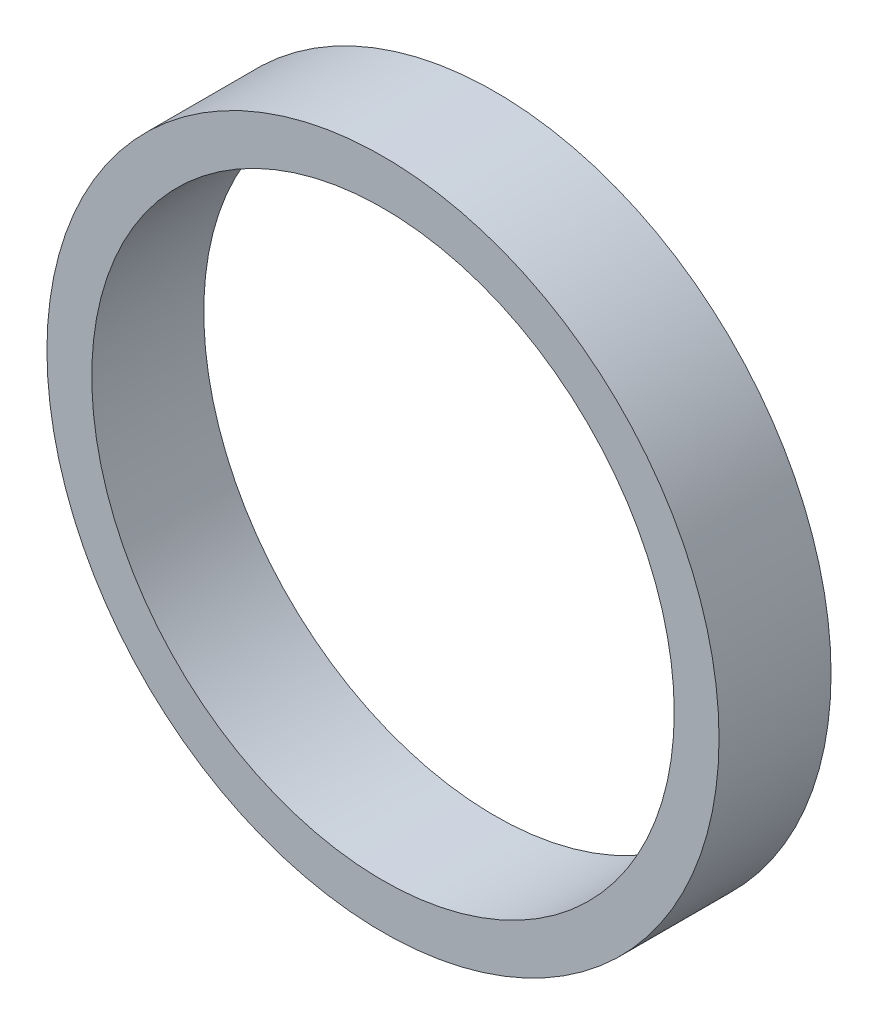
SolidWorks part; units mm, degrees
ref_plane "Alzado" through (0, 0, 0) normal (0, 0, 1) x (1, 0, 0)
ref_plane "Planta" through (0, 0, 0) normal (0, 1, 0) x (1, 0, 0)
ref_plane "Vista lateral" through (0, 0, 0) normal (1, 0, 0) x (0, 0, -1)
sketch "Croquis1" plane through (0, 0, 0) normal (0, 0, 1) x (1, 0, 0)
  circle A0 centre (0, 0) radius 1.3
  circle A1 centre (0, 0) radius 1.5
  dimension "D1" = 2.6
  dimension "D2" = 3
extrude "Saliente-Extruir1" add sketch "Croquis1" along normal blind 0.5
